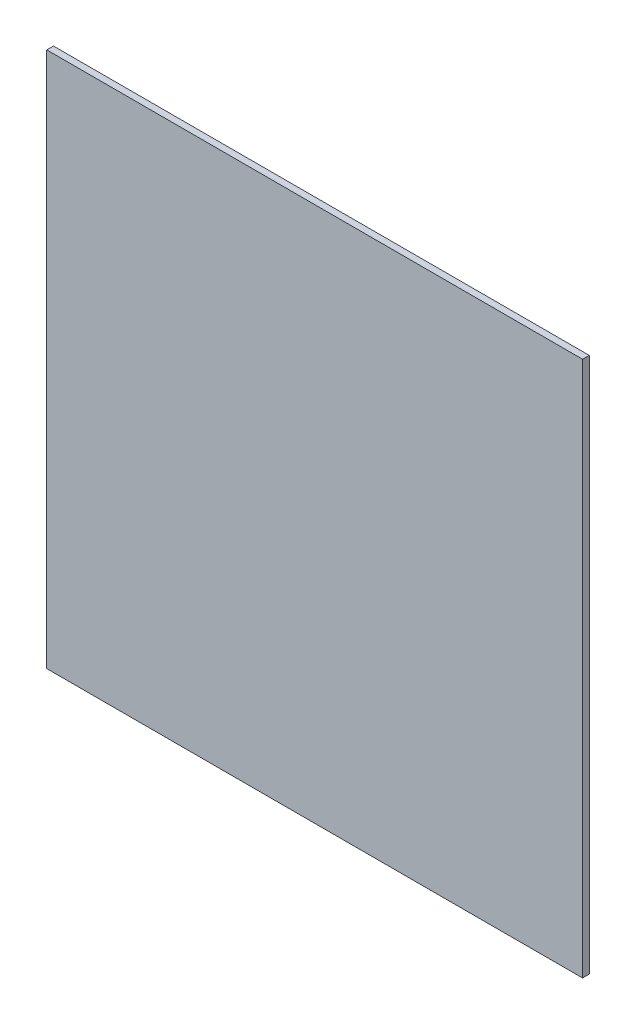
SolidWorks part; units mm, degrees
ref_plane "Front Plane" through (0, 0, 0) normal (0, 0, 1) x (1, 0, 0)
ref_plane "Top Plane" through (0, 0, 0) normal (0, 1, 0) x (1, 0, 0)
ref_plane "Right Plane" through (0, 0, 0) normal (1, 0, 0) x (0, 0, -1)
sketch "Sketch1" plane through (0, 0, 0) normal (0, 0, 1) x (1, 0, 0)
  line L1 (0, 0) -> (203.2, 0)
  line L2 (0, 0) -> (0, 203.2)
  line L3 (0, 203.2) -> (203.2, 203.2)
  line L4 (203.2, 0) -> (203.2, 203.2)
  dimension "D1" = 203.2
  dimension "D2" = 203.2
extrude "Boss-Extrude1" add sketch "Sketch1" along normal blind 2.54
